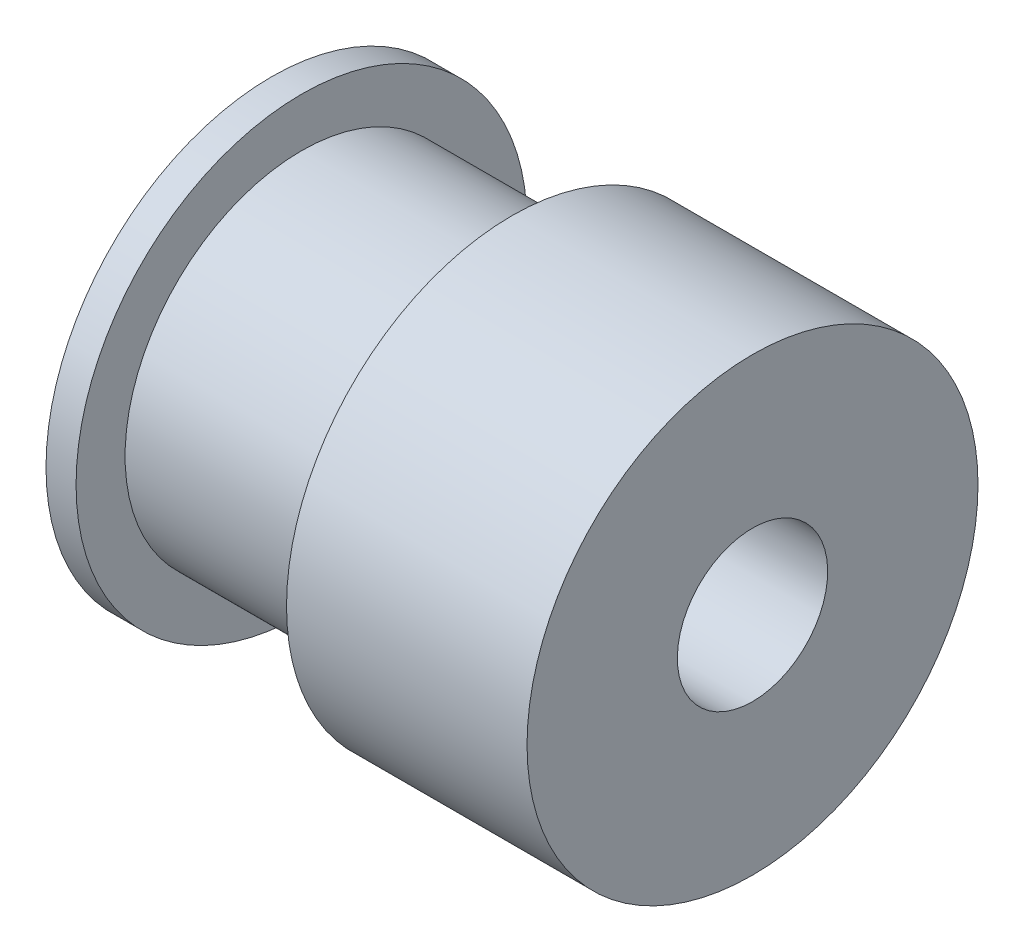
SolidWorks part; units mm, degrees
ref_plane "Front Plane" through (0, 0, 0) normal (0, 0, 1) x (1, 0, 0)
ref_plane "Top Plane" through (0, 0, 0) normal (0, 1, 0) x (1, 0, 0)
ref_plane "Right Plane" through (0, 0, 0) normal (1, 0, 0) x (0, 0, -1)
sketch "Sketch1" plane through (0, 0, 0) normal (0, 0, 1) x (1, 0, 0)
  line L0 (0, 0) -> (-7, 0)
  line L1 (-7, 0) -> (-16, 0)
  line L2 (-16, 0) -> (-16, 7.5)
  line L3 (-16, 7.5) -> (-15, 7.5)
  line L4 (-15, 7.5) -> (-15, 5.87)
  line L5 (-15, 5.87) -> (-8, 5.87)
  line L6 (-8, 5.87) -> (-8, 7.5)
  line L7 (-8, 7.5) -> (-7, 7.5)
  line L8 (-7, 7.5) -> (-7, 0)
  line L9 (0, 0) -> (0, 7.5)
  line L10 (0, 7.5) -> (-7, 7.5)
  dimension "D1" = 7
  dimension "D2" = 9
  dimension "D3" = 7.5
  dimension "D4" = 1
  dimension "D5" = 1.63
  dimension "D6" = 7
  dimension "D7" = 1
  dimension "D8" = 1.63
  dimension "D9" = 7.5
revolve "Revolve1" add sketch "Sketch1" angle 360 about L1
sketch "Sketch2" plane through (-16, 0, 0) normal (-1, 0, 0) x (0, 0, 1)
  circle A0 centre (0, 0) radius 2.5
  dimension "D1" = 5
extrude "Cut-Extrude1" cut sketch "Sketch2" against normal through all both and the other way through all
